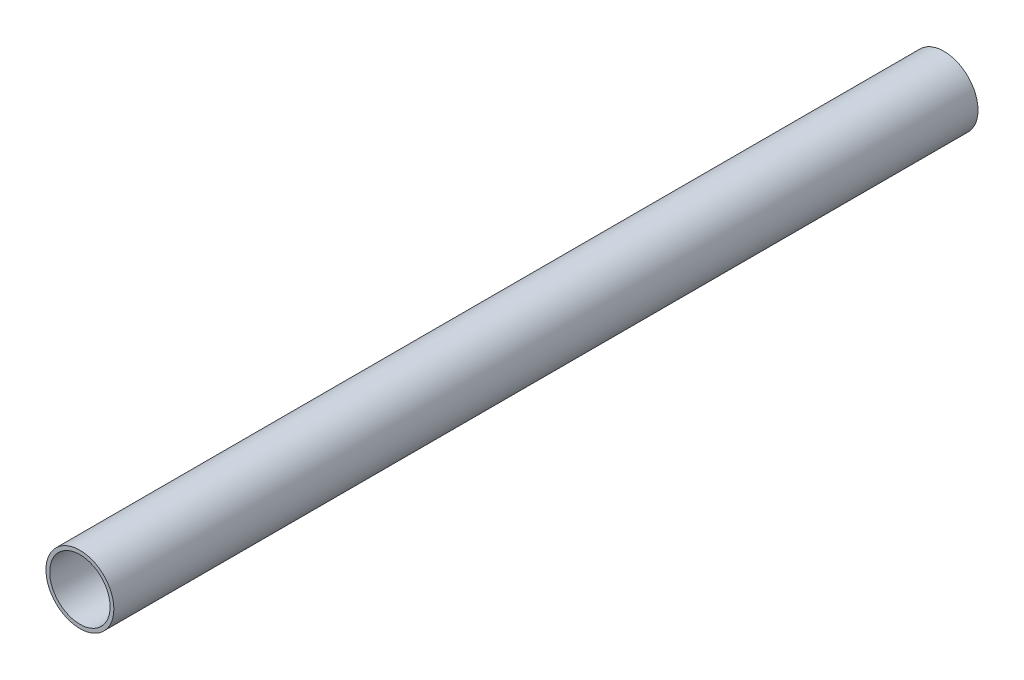
SolidWorks part; units mm, degrees
ref_plane "Płaszczyzna przednia" through (0, 0, 0) normal (0, 0, 1) x (1, 0, 0)
ref_plane "Płaszczyzna górna" through (0, 0, 0) normal (0, 1, 0) x (1, 0, 0)
ref_plane "Płaszczyzna prawa" through (0, 0, 0) normal (1, 0, 0) x (0, 0, -1)
sketch "Szkic1" plane through (0, 0, 0) normal (0, 0, 1) x (1, 0, 0)
  circle A0 centre (0, 0) radius 12
  circle A1 centre (0, 0) radius 13.5
  dimension "D1" = 24
  dimension "D2" = 27
extrude "Dodanie-wyciągnięcie1" add sketch "Szkic1" along normal blind 343.5
